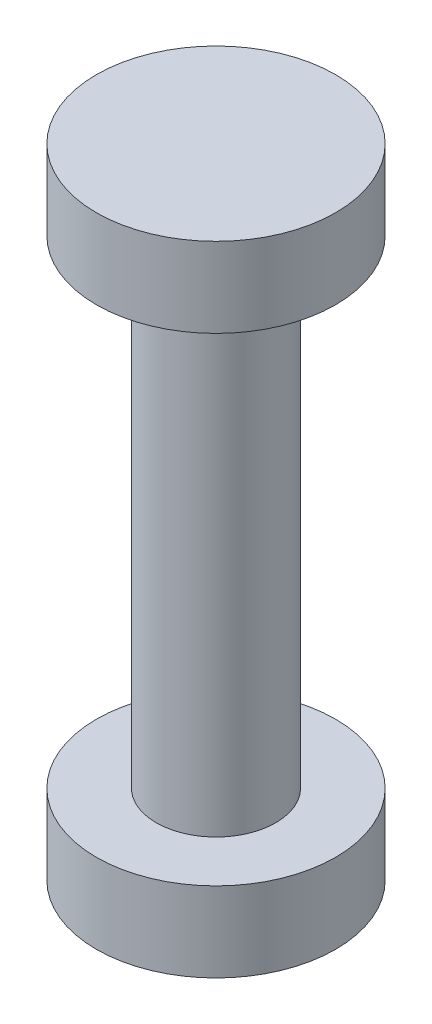
SolidWorks part; units mm, degrees
material "AISI 1020"
ref_plane "Plano frontal" through (0, 0, 0) normal (0, 0, 1) x (1, 0, 0)
ref_plane "Plano superior" through (0, 0, 0) normal (0, 1, 0) x (1, 0, 0)
ref_plane "Plano direito" through (0, 0, 0) normal (1, 0, 0) x (0, 0, -1)
sketch "Esboço1" plane through (0, 0, 0) normal (0, 0, 1) x (1, 0, 0)
  line L0 (0, 0) -> (0, 8) construction
  line L1 (0, 8) -> (3, 8)
  line L2 (3, 8) -> (3, 6)
  line L3 (3, 6) -> (1.5, 6)
  line L4 (1.5, 6) -> (1.5, -6)
  line L5 (0, 0) -> (1.5, 0) construction
  line L6 (3, -6) -> (1.5, -6)
  line L7 (3, -8) -> (3, -6)
  line L8 (0, -8) -> (3, -8)
  line L9 (0, 8) -> (0, -8)
  dimension "D1" = 3
  dimension "D2" = 6
  dimension "D3" = 6
  dimension "D4" = 2
revolve "Revolução1" add sketch "Esboço1" angle 360 about L9
